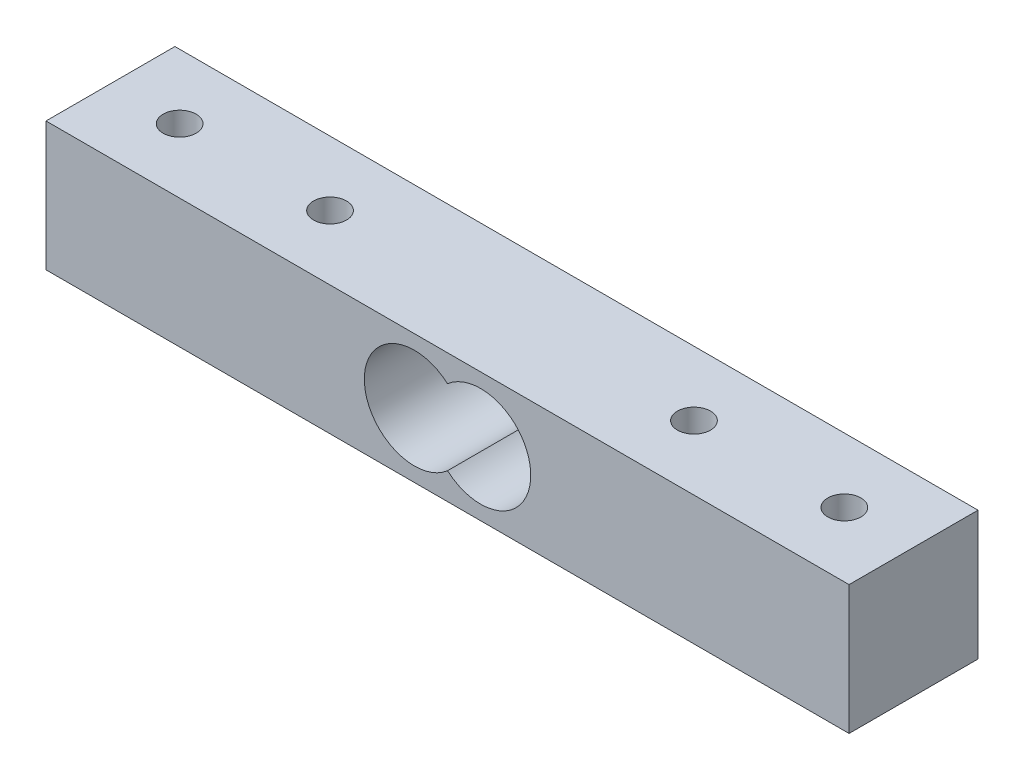
SolidWorks part; units mm, degrees
ref_plane "Front Plane" through (0, 0, 0) normal (0, 0, 1) x (1, 0, 0)
ref_plane "Top Plane" through (0, 0, 0) normal (0, 1, 0) x (1, 0, 0)
ref_plane "Right Plane" through (0, 0, 0) normal (1, 0, 0) x (0, 0, -1)
sketch "Çizim1" plane through (0, 0, 0) normal (0, 0, 1) x (1, 0, 0)
  line L0 (3.3, 0) -> (-3.3, 0) construction
  line L1 (-40.05, -6.43) -> (40.05, -6.43)
  line L2 (-40.05, -6.43) -> (-40.05, 6.43)
  line L3 (-40.05, 6.43) -> (40.05, 6.43)
  line L4 (40.05, -6.43) -> (40.05, 6.43)
  line L5 (-40.05, -6.43) -> (40.05, 6.43) construction
  line L6 (-40.05, 6.43) -> (40.05, -6.43) construction
  line L7 (0, 6.43) -> (0, 3.7563) construction
  line L8 (0, -3.7563) -> (0, -6.43) construction
  line L9 (-3.3, 5) -> (-3.3, 0) construction
  arc A0 (0, 3.7563) -> (0, -3.7563) centre (-3.3, 0) ccw
  arc A1 (0, 3.7563) -> (0, -3.7563) centre (3.3, 0) cw
  point P0 (0, 0)
  point P12 (0, 0)
  dimension "D1" = 12.86
  dimension "D4" = 10
  dimension "D2" = 80.1
  dimension "D3" = 3.3
extrude "Yükseklik-Ekstrüzyon2" add sketch "Çizim1" along normal mid plane 12.86
sketch "Çizim3" plane through (0, 6.43, 0) normal (0, 1, 0) x (1, 0, 0)
  line L0 (33.15, 0) -> (-33.15, 0) construction
  line L1 (-40.05, -6.43) -> (-40.05, 6.43) construction
  line L2 (0, 6.43) -> (0, -6.43) construction
  line L3 (40.05, 6.43) -> (-40.05, 6.43) construction
  point P1 (-33.15, 0)
  point P5 (-18.15, 0)
  point P11 (18.15, 0)
  point P12 (33.15, 0)
  point P13 (0, 0)
  point P20 (-33.15, 0)
  point P24 (33.15, 0)
  dimension "D1" = 6.9
  dimension "D2" = 15
sketch "Çizim7" plane through (0, 6.43, 0) normal (0, 1, 0) x (1, 0, 0)
  point P0 (-33.15, 0)
  point P3 (-18.15, 0)
  point P6 (18.15, 0)
  point P9 (33.15, 0)
hole_wizard "M4 Tapped Hole1" positions "Çizim7" profile "Çizim8" tap size "M4" standard "ISO" end condition through all
sketch "Çizim8" plane through (-33.15, 6.43, 0) normal (1, 0, 0) x (0, 0, 1)
  line L0 (0, 0) -> (0, 12.86)
  line L1 (0, 12.86) -> (2.025, 12.86)
  line L2 (1.65, 12.485) -> (1.65, 0)
  line L5 (1.65, 0) -> (0, 0)
  line L7 (2.025, 12.86) -> (1.65, 12.485)
  line L8 (-2.025, 12.86) -> (-1.65, 12.485) construction
  line L11 (0, -6.35) -> (0, 107.95) construction
  dimension "Thru Tap Drill Dia." = 3.3
  dimension "Thru Tap Drill Depth" = 12.86
  dimension "Far C'Sink Dia." = 4.05
  dimension "Far C'Sink Angle" = 90
cosmetic thread "Hole Thread1" parameters "D2"=4
cosmetic thread "Hole Thread2" parameters "D2"=4
cosmetic thread "Hole Thread3" parameters "D2"=4
cosmetic thread "Hole Thread4" parameters "D2"=4
